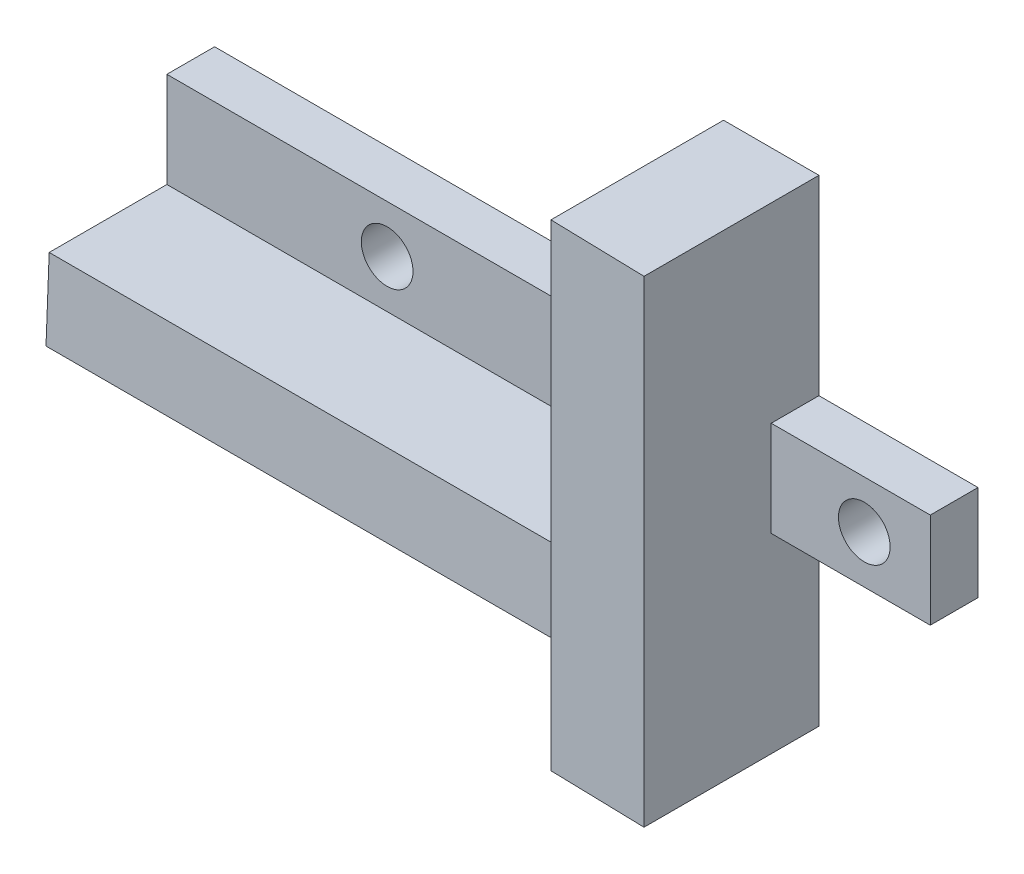
SolidWorks part; units mm, degrees
ref_plane "Plan de face" through (0, 0, 0) normal (0, 0, 1) x (1, 0, 0)
ref_plane "Plan de dessus" through (0, 0, 0) normal (0, 1, 0) x (1, 0, 0)
ref_plane "Plan de droite" through (0, 0, 0) normal (1, 0, 0) x (0, 0, -1)
sketch "Esquisse1" plane through (0, 0, 0) normal (0, 0, 1) x (1, 0, 0)
  line L0 (32, -6) -> (32, -18)
  line L1 (0, 0) -> (32, 0)
  line L2 (0, 0) -> (0, -6)
  line L3 (0, -6) -> (32, -6)
  line L5 (32, 12) -> (38, 12)
  line L6 (32, 12) -> (32, 0)
  line L7 (32, -18) -> (38, -18)
  line L8 (38, 12) -> (38, 0)
  line L9 (38, -6) -> (38, -18)
  line L10 (48, 0) -> (38, 0)
  line L11 (48, 0) -> (48, -6)
  line L12 (48, -6) -> (38, -6)
  point P9 (0, -3)
  point P15 (48, -3)
  dimension "D1" = 6
  dimension "D2" = 32
  dimension "D3" = 30
  dimension "D4" = 6
  dimension "D5" = 10
  dimension "D6" = 6
extrude "Boss.-Extru.1" add sketch "Esquisse1" along normal blind 3
sketch "Esquisse2" plane through (0, 0, 3) normal (0, 0, 1) x (1, 0, 0)
  line L0 (0, 0) -> (0, -6) construction
  circle A0 centre (13.85, -3) radius 1.625
  circle A1 centre (43.85, -3) radius 1.625
  point P8 (0, -3)
  dimension "D1" = 3.25
  dimension "D2" = 3.25
  dimension "D3" = 13.85
  dimension "D4" = 30
extrude "Enlèv. mat.-Extru.1" cut sketch "Esquisse2" against normal through all
sketch "Esquisse3" plane through (0, 0, 3) normal (0, 0, 1) x (1, 0, 0)
  line L0 (0, 0) -> (0, -6) construction
  line L1 (38, 12) -> (32, 12)
  line L2 (38, 12) -> (38, -18)
  line L3 (38, -18) -> (32, -18)
  line L4 (32, 12) -> (32, -6)
  line L5 (32, -6) -> (0, -6)
  line L7 (32, -11) -> (0, -11)
  line L8 (0, -6) -> (0, -11)
  line L9 (32, -11) -> (32, -18)
  dimension "D1" = 5
extrude "Boss.-Extru.2" add sketch "Esquisse3" along normal blind 10 and the other way through all
sketch "Esquisse4" plane through (0, 0, 0) normal (-1, 0, 0) x (0, 0, 1)
  line L0 (13, -6) -> (13, -11)
  line L1 (13, -11) -> (10.6, -11)
  line L2 (0, -11) -> (13, -11) construction
  line L3 (10.6, -11) -> (10.4, -6)
  line L4 (3, -6) -> (13, -6) construction
  line L5 (10.4, -6) -> (13, -6)
  dimension "D1" = 2.6
  dimension "D2" = 2.4
extrude "Enlèv. mat.-Extru.2" cut sketch "Esquisse4" against normal blind 32
sketch "Esquisse7" plane through (0, 0, 13) normal (0, 0, 1) x (1, 0, 0)
  line L1 (38, 12) -> (32, 12)
  line L2 (38, 12) -> (38, -18)
  line L3 (38, -18) -> (32, -18)
  line L4 (32, 12) -> (32, -18)
extrude "Enlèv. mat.-Extru.4" cut sketch "Esquisse7" against normal blind 2
sketch "Esquisse8" plane through (0, -18, 0) normal (0, -1, 0) x (1, 0, 0)
  line L0 (32, 11) -> (32, 10.85)
  line L1 (32, 11) -> (32, 0) construction
  line L2 (32, 10.85) -> (38, 11)
  line L3 (38, 11) -> (32, 11)
  dimension "D1" = 0.15
extrude "Enlèv. mat.-Extru.5" cut sketch "Esquisse8" against normal blind 30
